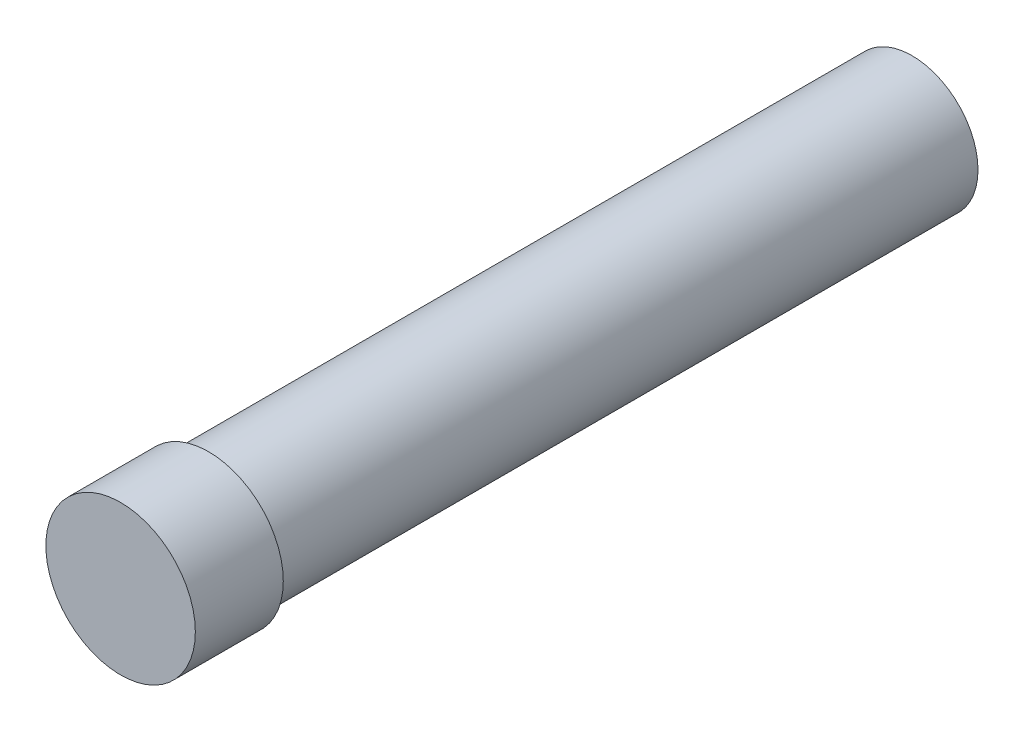
SolidWorks part; units mm, degrees
ref_plane "Ön Düzlem" through (0, 0, 0) normal (0, 0, 1) x (1, 0, 0)
ref_plane "Üst Düzlem" through (0, 0, 0) normal (0, 1, 0) x (1, 0, 0)
ref_plane "Sağ Düzlem" through (0, 0, 0) normal (1, 0, 0) x (0, 0, -1)
sketch "Çizim1" plane through (0, 0, 0) normal (0, 0, 1) x (1, 0, 0)
  circle A0 centre (0, 0) radius 75
extrude "Yükseklik-Ekstrüzyon1" add sketch "Çizim1" along normal blind 800
sketch "Çizim2" plane through (0, 0, 800) normal (0, 0, 1) x (1, 0, 0)
  circle A0 centre (0, 0) radius 85
extrude "Yükseklik-Ekstrüzyon2" add sketch "Çizim2" along normal blind 100
